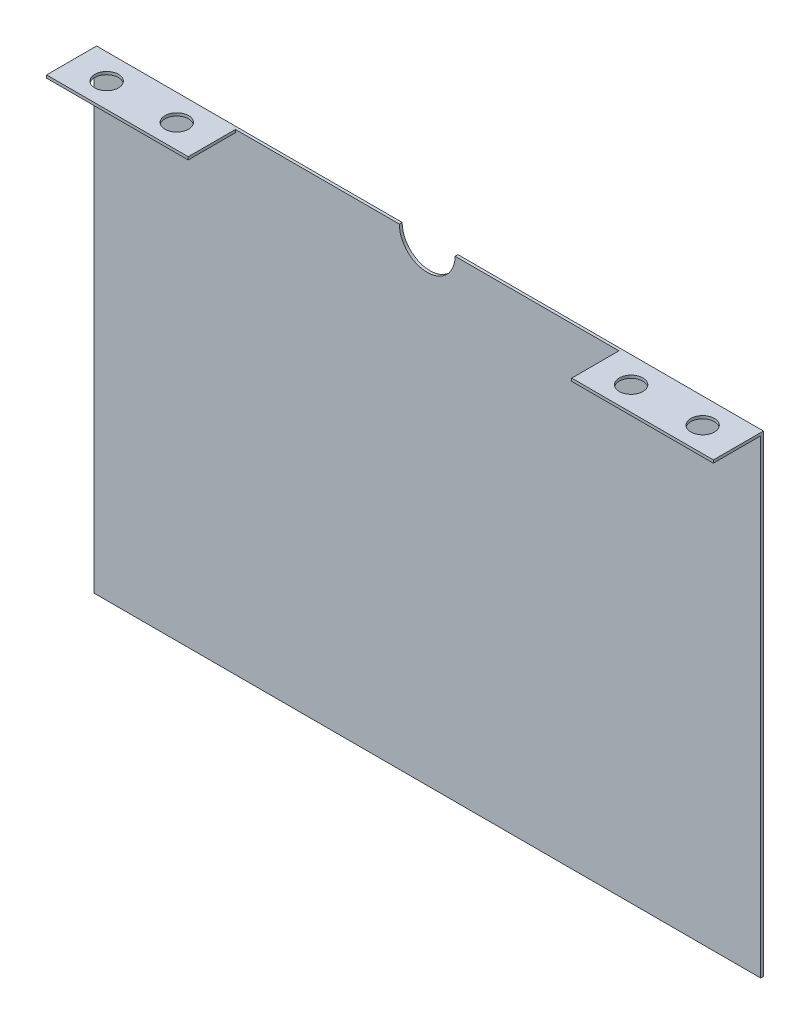
SolidWorks part; units mm, degrees
material "Plain Carbon Steel"
ref_plane "Front Plane" through (0, 0, 0) normal (0, 0, 1) x (1, 0, 0)
ref_plane "Top Plane" through (0, 0, 0) normal (0, 1, 0) x (1, 0, 0)
ref_plane "Right Plane" through (0, 0, 0) normal (1, 0, 0) x (0, 0, -1)
sketch "Sketch1" plane through (0, 0, 0) normal (0, 0, 1) x (1, 0, 0)
  line L0 (0, 0) -> (0, 177.8) construction
  line L1 (-179.3189, 177.8) -> (-15, 177.8)
  line L2 (-179.3189, 177.8) -> (-179.3189, -76.2)
  line L3 (-179.3189, -76.2) -> (179.3189, -76.2)
  line L4 (179.3189, 177.8) -> (179.3189, -76.2)
  line L5 (-179.3189, 0) -> (179.3189, 0) construction
  line L6 (15, 177.8) -> (179.3189, 177.8)
  line L7 (-15, 177.8) -> (15, 177.8) construction
  arc A0 (15, 177.8) -> (-15, 177.8) centre (0, 177.8) cw
  dimension "D3" = 15
  dimension "D1" = 358.6378
  dimension "D2" = 177.8
  dimension "D4" = 179.3189
  dimension "D5" = 76.2
extrude "Bottom Center Casing" add sketch "Sketch1" along normal blind 1.5189
sketch "Sketch2" plane through (0, 0, 1.5189) normal (0, 0, 1) x (1, 0, 0)
  line L0 (-15, 177.8) -> (-179.3189, 177.8) construction
  line L1 (179.3189, 177.8) -> (15, 177.8) construction
  line L2 (0, 177.8) -> (0, 144.5) construction
  line L3 (-97.1595, 177.8) -> (97.1595, 177.8) construction
  point P0 (-97.1595, 177.8)
  point P3 (-97.1595, 177.8)
  point P4 (97.1595, 177.8)
  point P7 (97.1595, 177.8)
  point P12 (0, 177.8)
  dimension "D1" = 33.3
sketch "Sketch3" plane through (0, 0, 1.5189) normal (0, 0, 1) x (1, 0, 0)
  line L1 (-179.3189, 177.8) -> (-103.1189, 177.8)
  line L2 (-179.3189, 177.8) -> (-179.3189, 176.2811)
  line L3 (-179.3189, 176.2811) -> (-103.1189, 176.2811)
  line L4 (-103.1189, 177.8) -> (-103.1189, 176.2811)
  line L5 (179.3189, 177.8) -> (103.1189, 177.8)
  line L6 (179.3189, 177.8) -> (179.3189, 176.2811)
  line L7 (179.3189, 176.2811) -> (103.1189, 176.2811)
  line L8 (103.1189, 177.8) -> (103.1189, 176.2811)
  dimension "D1" = 76.2
  dimension "D2" = 1.5189
  dimension "D3" = 1.5189
  dimension "D4" = 76.2
extrude "Boss-Extrude1" add sketch "Sketch3" along normal blind 25.4
sketch "Sketch4" plane through (0, 177.8, 0) normal (0, 1, 0) x (1, 0, 0)
  line L0 (-179.3189, -13.4595) -> (-103.1189, -14.2189) construction
  line L1 (-179.3189, -26.9189) -> (-179.3189, 0) construction
  line L2 (-103.1189, -26.9189) -> (-103.1189, -1.5189) construction
  line L4 (0, -55) -> (0, 55) construction
  circle A0 centre (-160.2689, -13.6493) radius 6.35
  circle A1 centre (-122.1689, -14.0291) radius 6.35
  circle A2 centre (122.1689, -14.0291) radius 6.35
  circle A3 centre (160.2689, -13.6493) radius 6.35
  dimension "D1" = 12.7
  dimension "D2" = 19.05
  dimension "D3" = 38.1
extrude "Cut-Extrude1" cut sketch "Sketch4" against normal blind 25.4
